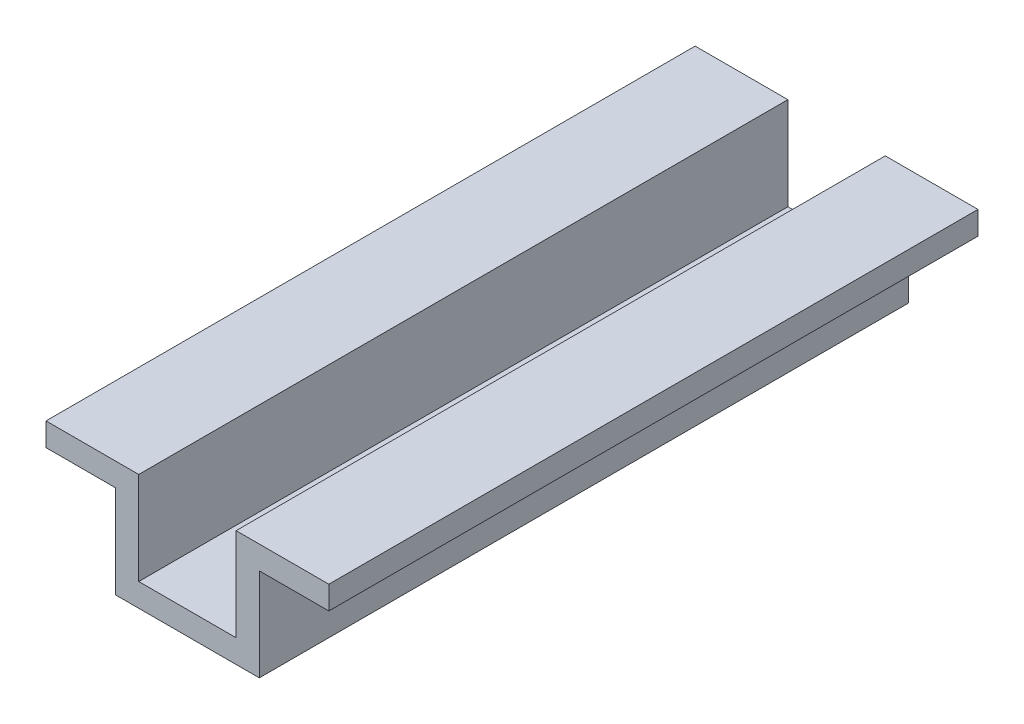
SolidWorks part; units mm, degrees
ref_plane "Front Plane" through (0, 0, 0) normal (0, 0, 1) x (1, 0, 0)
ref_plane "Top Plane" through (0, 0, 0) normal (0, 1, 0) x (1, 0, 0)
ref_plane "Right Plane" through (0, 0, 0) normal (1, 0, 0) x (0, 0, -1)
sketch "Sketch1" plane through (0, 0, 0) normal (0, 0, 1) x (1, 0, 0)
  line L0 (21, 20) -> (41, 20)
  line L1 (0, 0) -> (21, 0)
  line L2 (0, 0) -> (0, 20)
  line L4 (21, 0) -> (21, 20)
  line L5 (0, 20) -> (-20, 20)
  dimension "D1" = 21
  dimension "D2" = 20
  dimension "D3" = 20
  dimension "D4" = 20
extrude "Extrude-Thin1" add sketch "Sketch1" along normal blind 140 thin
